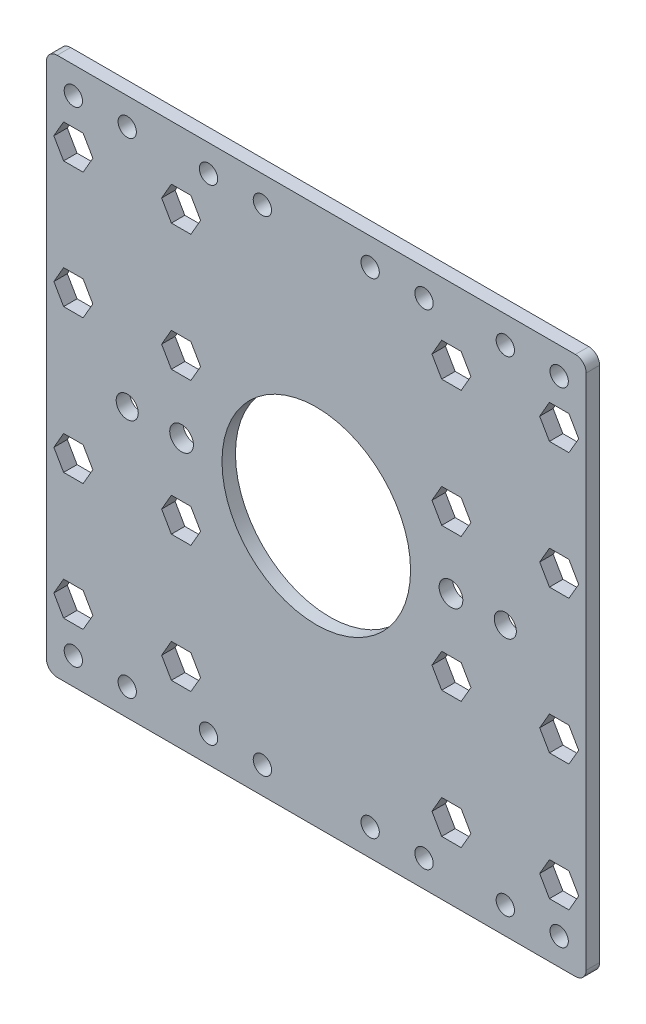
SolidWorks part; units mm, degrees
ref_plane "Ebene vorne" through (0, 0, 0) normal (0, 0, 1) x (1, 0, 0)
ref_plane "Ebene oben" through (0, 0, 0) normal (0, 1, 0) x (1, 0, 0)
ref_plane "Ebene rechts" through (0, 0, 0) normal (1, 0, 0) x (0, 0, -1)
sketch "Skizze1" plane through (0, 0, 0) normal (0, 0, 1) x (1, 0, 0)
  line L0 (9.9144, -80) -> (120, -80) construction
  line L1 (10, 0) -> (10, -80) construction
  line L2 (0, -85) -> (120, -85) construction
  line L3 (9.9144, -80) -> (9.9144, 0)
  line L4 (60, 0) -> (60, -80) construction
  line L5 (0, -40) -> (120, -40) construction
  line L6 (35, 0) -> (35, -80) construction
  line L7 (9.9144, -80) -> (9.9144, -88)
  line L8 (11.9144, 10) -> (108.0856, 10)
  line L9 (11.9144, -90) -> (108.0856, -90)
  line L10 (9.9144, 0) -> (9.9144, 8)
  line L11 (101.4627, -76.7488) -> (103.2742, -79.8864)
  line L12 (103.2742, -79.8864) -> (106.8971, -79.8864)
  line L13 (50, 0) -> (50, -80) construction
  line L14 (33.1073, -56.3812) -> (31.3002, -53.2512)
  line L15 (18.5373, -3.2512) -> (16.7258, -0.1136)
  line L16 (16.7258, -0.1136) -> (13.1029, -0.1136)
  line L17 (13.1029, -0.1136) -> (11.2915, -3.2512)
  line L18 (11.2915, -3.2512) -> (13.1029, -6.3887)
  line L19 (13.1029, -6.3887) -> (16.7258, -6.3887)
  line L20 (16.7258, -6.3887) -> (18.5373, -3.2512)
  line L21 (38.5286, -3.2512) -> (36.7215, -0.1212)
  line L22 (36.7215, -0.1212) -> (33.1073, -0.1212)
  line L23 (33.1073, -0.1212) -> (31.3002, -3.2512)
  line L24 (31.3002, -3.2512) -> (33.1073, -6.3812)
  line L25 (33.1073, -6.3812) -> (36.7215, -6.3812)
  line L26 (36.7215, -6.3812) -> (38.5286, -3.2512)
  line L27 (18.5286, -26.6744) -> (16.7215, -23.5444)
  line L28 (16.7215, -23.5444) -> (13.1073, -23.5444)
  line L29 (13.1073, -23.5444) -> (11.3002, -26.6744)
  line L30 (11.3002, -26.6744) -> (13.1073, -29.8044)
  line L31 (13.1073, -29.8044) -> (16.7215, -29.8044)
  line L32 (16.7215, -29.8044) -> (18.5286, -26.6744)
  line L33 (31.3002, -26.7488) -> (33.1073, -29.8788)
  line L34 (33.1073, -29.8788) -> (36.7215, -29.8788)
  line L35 (36.7215, -29.8788) -> (38.5286, -26.7488)
  line L36 (38.5286, -26.7488) -> (36.7215, -23.6188)
  line L37 (36.7215, -23.6188) -> (33.1073, -23.6188)
  line L38 (33.1073, -23.6188) -> (31.3002, -26.7488)
  line L39 (36.7215, -56.3812) -> (33.1073, -56.3812)
  line L40 (38.5286, -53.2512) -> (36.7215, -56.3812)
  line L41 (36.7215, -50.1212) -> (38.5286, -53.2512)
  line L42 (33.1073, -50.1212) -> (36.7215, -50.1212)
  line L43 (31.3002, -53.2512) -> (33.1073, -50.1212)
  line L44 (16.7215, -50.1956) -> (18.5286, -53.3256)
  line L45 (13.1073, -50.1956) -> (16.7215, -50.1956)
  line L46 (11.3002, -53.3256) -> (13.1073, -50.1956)
  line L47 (13.1073, -56.4556) -> (11.3002, -53.3256)
  line L48 (16.7215, -56.4556) -> (13.1073, -56.4556)
  line L49 (18.5286, -53.3256) -> (16.7215, -56.4556)
  line L50 (36.7215, -73.6188) -> (38.5286, -76.7488)
  line L51 (33.1073, -73.6188) -> (36.7215, -73.6188)
  line L52 (31.3002, -76.7488) -> (33.1073, -73.6188)
  line L53 (33.1073, -79.8788) -> (31.3002, -76.7488)
  line L54 (36.7215, -79.8788) -> (33.1073, -79.8788)
  line L55 (38.5286, -76.7488) -> (36.7215, -79.8788)
  line L56 (16.7258, -73.6113) -> (18.5373, -76.7488)
  line L57 (13.1029, -73.6113) -> (16.7258, -73.6113)
  line L58 (11.2915, -76.7488) -> (13.1029, -73.6113)
  line L59 (13.1029, -79.8864) -> (11.2915, -76.7488)
  line L60 (16.7258, -79.8864) -> (13.1029, -79.8864)
  line L61 (18.5373, -76.7488) -> (16.7258, -79.8864)
  line L62 (106.8971, -79.8864) -> (108.7085, -76.7488)
  line L63 (108.7085, -76.7488) -> (106.8971, -73.6113)
  line L64 (106.8971, -73.6113) -> (103.2742, -73.6113)
  line L65 (103.2742, -73.6113) -> (101.4627, -76.7488)
  line L66 (81.4714, -76.7488) -> (83.2785, -79.8788)
  line L67 (83.2785, -79.8788) -> (86.8927, -79.8788)
  line L68 (86.8927, -79.8788) -> (88.6998, -76.7488)
  line L69 (88.6998, -76.7488) -> (86.8927, -73.6188)
  line L70 (86.8927, -73.6188) -> (83.2785, -73.6188)
  line L71 (83.2785, -73.6188) -> (81.4714, -76.7488)
  line L72 (101.4714, -53.3256) -> (103.2785, -56.4556)
  line L73 (103.2785, -56.4556) -> (106.8927, -56.4556)
  line L74 (106.8927, -56.4556) -> (108.6998, -53.3256)
  line L75 (108.6998, -53.3256) -> (106.8927, -50.1956)
  line L76 (106.8927, -50.1956) -> (103.2785, -50.1956)
  line L77 (103.2785, -50.1956) -> (101.4714, -53.3256)
  line L78 (88.6998, -53.2512) -> (86.8927, -50.1212)
  line L79 (86.8927, -50.1212) -> (83.2785, -50.1212)
  line L80 (83.2785, -50.1212) -> (81.4714, -53.2512)
  line L81 (81.4714, -53.2512) -> (83.2785, -56.3812)
  line L82 (83.2785, -56.3812) -> (86.8927, -56.3812)
  line L83 (86.8927, -23.6188) -> (88.6998, -26.7488)
  line L84 (83.2785, -23.6188) -> (86.8927, -23.6188)
  line L85 (81.4714, -26.7488) -> (83.2785, -23.6188)
  line L86 (83.2785, -29.8788) -> (81.4714, -26.7488)
  line L87 (86.8927, -29.8788) -> (83.2785, -29.8788)
  line L88 (88.6998, -26.7488) -> (86.8927, -29.8788)
  line L89 (103.2785, -29.8044) -> (101.4714, -26.6744)
  line L90 (106.8927, -29.8044) -> (103.2785, -29.8044)
  line L91 (108.6998, -26.6744) -> (106.8927, -29.8044)
  line L92 (106.8927, -23.5444) -> (108.6998, -26.6744)
  line L93 (103.2785, -23.5444) -> (106.8927, -23.5444)
  line L94 (101.4714, -26.6744) -> (103.2785, -23.5444)
  line L95 (83.2785, -6.3812) -> (81.4714, -3.2512)
  line L96 (86.8927, -6.3812) -> (83.2785, -6.3812)
  line L97 (88.6998, -3.2512) -> (86.8927, -6.3812)
  line L98 (86.8927, -0.1212) -> (88.6998, -3.2512)
  line L99 (83.2785, -0.1212) -> (86.8927, -0.1212)
  line L100 (81.4714, -3.2512) -> (83.2785, -0.1212)
  line L101 (103.2742, -6.3887) -> (101.4627, -3.2512)
  line L102 (106.8971, -6.3887) -> (103.2742, -6.3887)
  line L103 (108.7085, -3.2512) -> (106.8971, -6.3887)
  line L104 (106.8971, -0.1136) -> (108.7085, -3.2512)
  line L105 (103.2742, -0.1136) -> (106.8971, -0.1136)
  line L106 (101.4627, -3.2512) -> (103.2742, -0.1136)
  line L107 (86.8927, -56.3812) -> (88.6998, -53.2512)
  line L108 (110.0856, 0) -> (110.0856, 8)
  line L109 (110.0856, -80) -> (110.0856, -88)
  line L110 (110.0856, -80) -> (110.0856, 0)
  circle A0 centre (60, -40) radius 17.5
  circle A1 centre (35, -40) radius 2.2
  circle A2 centre (50, -85) radius 1.7
  circle A3 centre (24.9144, -40) radius 2.05
  circle A4 centre (40, -85) radius 1.7
  circle A5 centre (95.0856, -85) radius 1.7
  circle A6 centre (24.9144, -85) radius 1.7
  circle A7 centre (14.9144, -85) radius 1.7
  circle A8 centre (105.0856, -85) radius 1.7
  circle A9 centre (40, 5) radius 1.7
  circle A10 centre (50, 5) radius 1.7
  circle A11 centre (105.0856, -76.7488) radius 3.1375 construction
  circle A12 centre (85.0856, -76.7488) radius 3.13 construction
  circle A13 centre (105.0856, -53.3256) radius 3.13 construction
  circle A14 centre (85.0856, -53.2512) radius 3.13 construction
  circle A15 centre (70, 5) radius 1.7
  circle A16 centre (80, 5) radius 1.7
  circle A17 centre (95.0856, 5) radius 1.7
  circle A18 centre (105.0856, 5) radius 1.7
  arc A19 (11.9144, -90) -> (9.9144, -88) centre (11.9144, -88) cw
  arc A20 (108.0856, -90) -> (110.0856, -88) centre (108.0856, -88) ccw
  circle A21 centre (80, -85) radius 1.7
  circle A22 centre (95.0856, -40) radius 2.05
  circle A23 centre (70, -85) radius 1.7
  circle A24 centre (85, -40) radius 2.2
  circle A25 centre (24.9144, 5) radius 1.7
  circle A26 centre (14.9144, 5) radius 1.7
  arc A27 (108.0856, 10) -> (110.0856, 8) centre (108.0856, 8) cw
  arc A28 (11.9144, 10) -> (9.9144, 8) centre (11.9144, 8) ccw
  circle A30 centre (34.9144, -53.2512) radius 3.13 construction
  circle A31 centre (14.9144, -53.3256) radius 3.13 construction
  circle A32 centre (34.9144, -76.7488) radius 3.13 construction
  circle A33 centre (14.9144, -76.7488) radius 3.1375 construction
  circle A34 centre (20, -85) radius 1.7 [skipped]
  circle A35 centre (30, -85) radius 1.7 [skipped]
  point P16 (60, 10)
  point P59 (9.9144, -90)
  point P176 (60, -90)
  point P187 (110.0856, -90)
  point P190 (110.0856, 10)
  point P193 (9.9144, 10)
  dimension "D1" = 4
  dimension "D2" = 2
extrude "Aufsatz-Linear austragen1" add sketch "Skizze1" along normal blind 2.5
